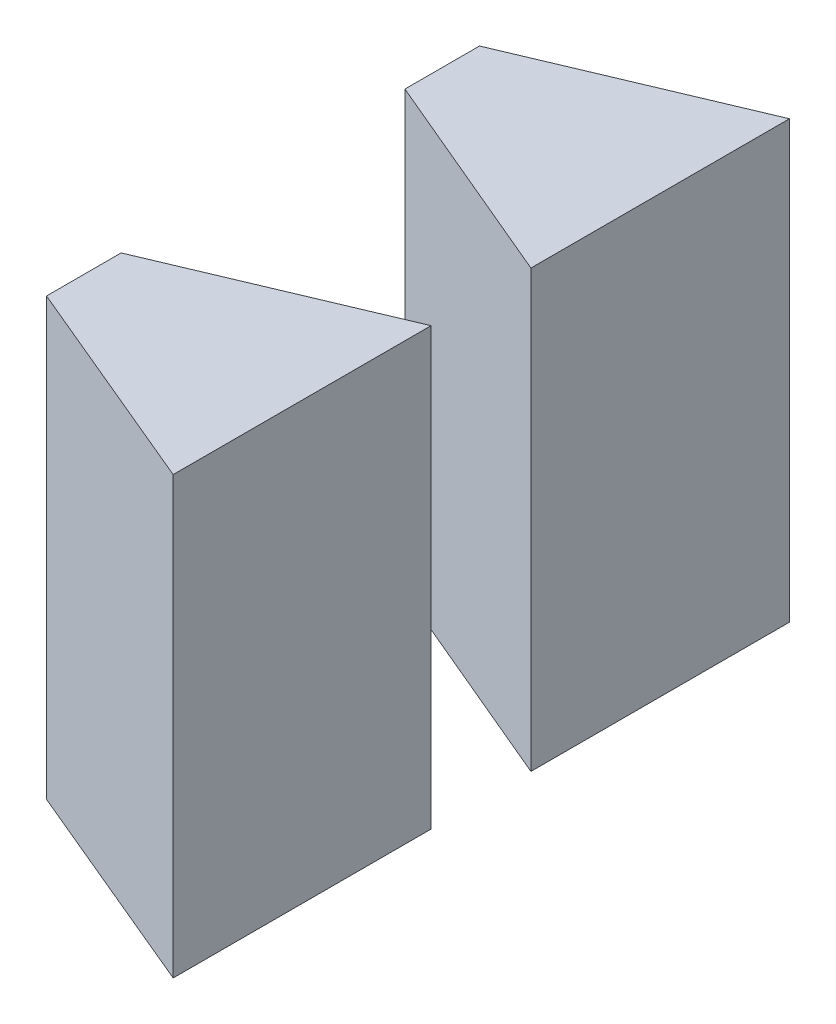
SolidWorks part; units mm, degrees
ref_plane "Front Plane" through (0, 0, 0) normal (0, 0, 1) x (1, 0, 0)
ref_plane "Top Plane" through (0, 0, 0) normal (0, 1, 0) x (1, 0, 0)
ref_plane "Right Plane" through (0, 0, 0) normal (1, 0, 0) x (0, 0, -1)
sketch "Sketch1" plane through (0, 0, 0) normal (0, 1, 0) x (1, 0, 0)
  line L1 (0, 0) -> (7.5, 0)
  line L2 (0, 0) -> (0, 27.66)
  line L3 (0, 27.66) -> (7.5, 27.66)
  line L4 (7.5, 0) -> (7.5, 27.66)
  dimension "D1" = 27.66
  dimension "D2" = 7.5
extrude "Boss-Extrude1" add sketch "Sketch1" along normal blind 25
sketch "Sketch2" plane through (0, 0, 0) normal (0, -1, 0) x (1, 0, 0)
  line L1 (0, 0) -> (7.5, 0)
  line L2 (0, 0) -> (0, -27.66)
  line L3 (0, -27.66) -> (7.5, -27.66)
  line L4 (7.5, 0) -> (7.5, -27.66)
extrude "Cut-Extrude1" cut sketch "Sketch2" against normal blind 10
sketch "Sketch3" plane through (0, 10, 0) normal (0, -1, 0) x (1, 0, 0)
  line L0 (0, -6.165) -> (0, -5.9482)
  line L1 (0, -5.9482) -> (7.5, -2.8054)
  line L2 (7.5, -2.8054) -> (7.5, -3.239)
  line L3 (0, -6.165) -> (7.5, -3)
  line L4 (0, 0) -> (0, -27.66) construction
  line L5 (7.5, -27.66) -> (7.5, 0) construction
  line L6 (7.5, -3) -> (7.5, -12.33)
  line L7 (7.5, -12.33) -> (0, -9.165)
  line L8 (0, -9.165) -> (0, -6.165)
  line L9 (0, -18.495) -> (7.5, -15.33)
  line L10 (7.5, -15.33) -> (7.5, -24.66)
  line L11 (7.5, -24.66) -> (0, -21.495)
  line L12 (0, -21.495) -> (0, -18.495)
  line L13 (7.5, -3.239) -> (0, -6.3818)
  line L14 (0, -6.3818) -> (0, -6.165)
  line L15 (7.5, -12.5471) -> (7.5, -12.1129)
  line L16 (7.5, -12.1129) -> (0, -8.9479)
  line L17 (0, -8.9479) -> (0, -9.3821)
  line L18 (0, -9.3821) -> (7.5, -12.5471)
  line L19 (0, -17.6267) -> (7.5, -14.4617)
  line L20 (7.5, -14.4617) -> (7.5, -15.5471)
  line L21 (7.5, -15.5471) -> (0, -18.7121)
  line L22 (0, -18.7121) -> (0, -17.6267)
  line L23 (7.5, -24.4429) -> (0, -21.2779)
  line L24 (0, -21.2779) -> (0, -21.7121)
  line L25 (0, -21.7121) -> (7.5, -24.8771)
  line L26 (7.5, -24.8771) -> (7.5, -24.4429)
  dimension "D1" = 9.33
  dimension "D2" = 9.33
  dimension "D3" = 3
  dimension "D4" = 3
  dimension "D5" = 6.165
  dimension "D6" = 9.33
  dimension "D7" = 3
  dimension "D8" = 3
  dimension "D9" = 0.4
  dimension "D10" = 0.2
  dimension "D12" = 0.4
  dimension "D13" = 0.2
  dimension "D14" = 1
  dimension "D15" = 0.2
  dimension "D16" = 0.2
  dimension "D17" = 0.4
extrude "Cut-Extrude2" cut sketch "Sketch3" against normal through all both and the other way through all contours L18 L3 L2 L1 | L13 L16 L3 L18 | L16 L18 L7 | L18 L16 L7 | L19 L18 L9 L16 | L18 L25 L16 L11 | L16 L23 L18 L11
sketch "Sketch4" plane through (0, 10, 0) normal (0, -1, 0) x (1, 0, 0)
  line L0 (0, 0) -> (7.5, 0)
  line L1 (7.5, 0) -> (7.5, -2.8054)
  line L2 (7.5, -2.8054) -> (0, -5.9482)
  line L3 (0, -5.9482) -> (0, 0)
  line L4 (0, -9.3821) -> (7.5, -12.5471)
  line L5 (7.5, -12.5471) -> (7.5, -14.7873)
  line L6 (7.5, -14.4617) -> (7.5, -12.5471) construction
  line L7 (7.5, -14.7873) -> (0, -17.6267)
  line L8 (0, -17.6267) -> (0, -9.3821)
  line L9 (0, -21.7121) -> (7.5, -24.8771)
  line L10 (0, -21.7121) -> (7.5, -24.8771) construction
  line L11 (7.5, -24.8771) -> (7.5, -27.66)
  line L12 (7.5, -27.66) -> (0, -27.66)
  line L13 (0, -27.66) -> (0, -21.7121)
extrude "Cut-Extrude3" cut sketch "Sketch4" against normal through all both and the other way through all contours L3 L0 L1 L2 | L8 L4 L5 L7 | L13 L9 L11 L12
